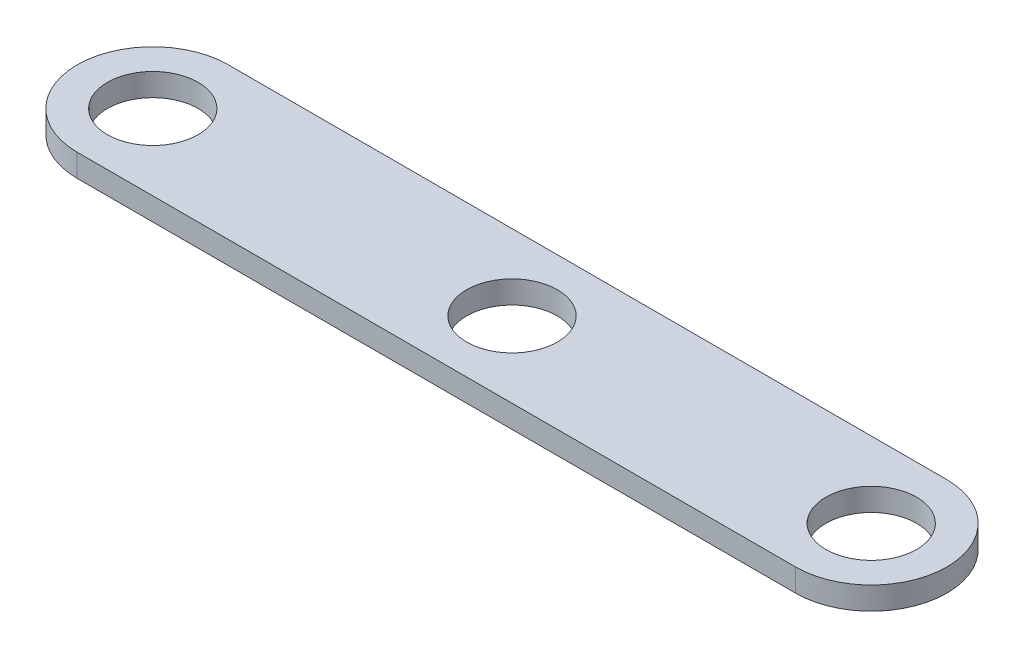
SolidWorks part; units mm, degrees
ref_plane "Front" through (0, 0, 0) normal (0, 0, 1) x (1, 0, 0)
ref_plane "Top" through (0, 0, 0) normal (0, 1, 0) x (1, 0, 0)
ref_plane "Right" through (0, 0, 0) normal (1, 0, 0) x (0, 0, -1)
sketch "Sketch1" plane through (0, 0, 0) normal (0, 1, 0) x (1, 0, 0)
  line L0 (-7.0926, 9.3269) -> (87.9074, 9.3269) construction
  line L1 (-7.0926, 19.3269) -> (87.9074, 19.3269)
  line L2 (-7.0926, -0.6731) -> (87.9074, -0.6731)
  arc A0 (-7.0926, 19.3269) -> (-7.0926, -0.6731) centre (-7.0926, 9.3269) ccw
  arc A1 (87.9074, -0.6731) -> (87.9074, 19.3269) centre (87.9074, 9.3269) ccw
  circle A2 centre (-7.0926, 9.3269) radius 6
  circle A3 centre (87.9074, 9.3269) radius 6
  point P2 (40.4074, 9.3269)
  dimension "D3" = 12
  dimension "D4" = 12
  dimension "D1" = 20
  dimension "D2" = 95
extrude "Boss-Extrude1" add sketch "Sketch1" along normal blind 3
sketch "Sketch2" plane through (0, 3, 0) normal (0, 1, 0) x (1, 0, 0)
  circle A0 centre (40.4074, 9.3269) radius 6
extrude "Cut-Extrude1" cut sketch "Sketch2" against normal through all
